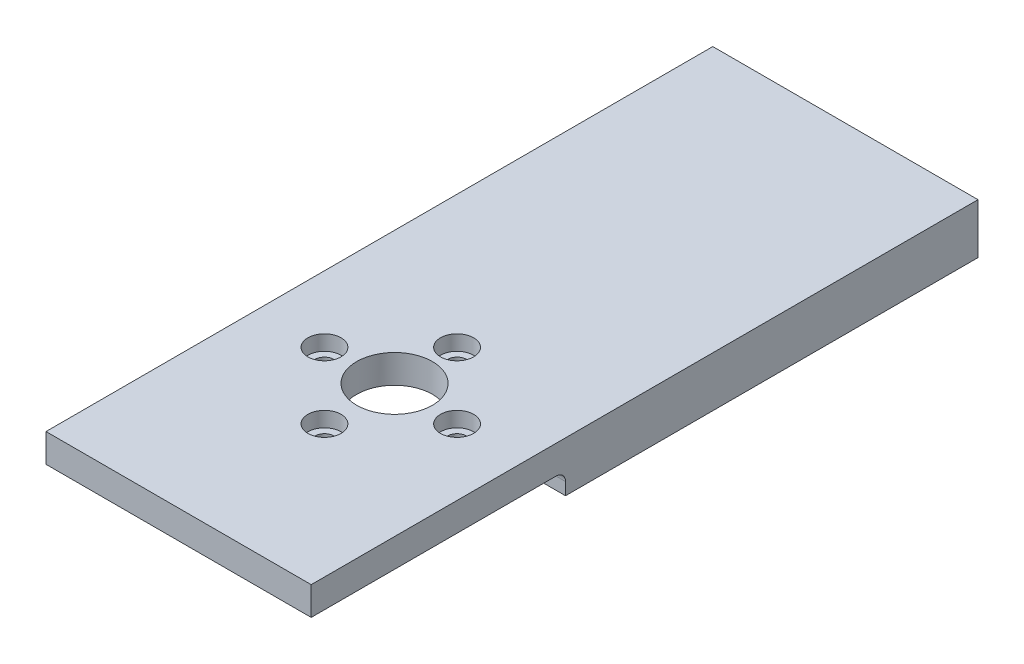
SolidWorks part; units mm, degrees
material "Custom Plastic"
ref_plane "Front Plane" through (0, 0, 0) normal (0, 0, 1) x (1, 0, 0)
ref_plane "Top Plane" through (0, 0, 0) normal (0, 1, 0) x (1, 0, 0)
ref_plane "Right Plane" through (0, 0, 0) normal (1, 0, 0) x (0, 0, -1)
sketch "Sketch1" plane through (0, 0, 0) normal (0, 1, 0) x (1, 0, 0)
  line L1 (-14, -35.2) -> (14, -35.2)
  line L2 (-14, -35.2) -> (-14, 35.2)
  line L3 (-14, 35.2) -> (14, 35.2)
  line L4 (14, -35.2) -> (14, 35.2)
  line L5 (-14, -35.2) -> (14, 35.2) construction
  line L6 (-14, 35.2) -> (14, -35.2) construction
  point P0 (0, 0)
  dimension "D1" = 70.4
  dimension "D2" = 28
extrude "Boss-Extrude1" add sketch "Sketch1" along normal blind 3
sketch "Sketch4" plane through (0, 3, 0) normal (0, 1, 0) x (1, 0, 0)
  line L0 (0, -2.5883) -> (0, -23.7562) construction
  line L1 (14, -35.2) -> (14, 35.2) construction
  circle A0 centre (7, -12.8) radius 1
  circle A1 centre (0, -19.8) radius 1
  circle A2 centre (-7, -12.8) radius 1
  circle A4 centre (0, -5.8) radius 1
  circle A9 centre (0, -12.8) radius 7 construction
  point P18 (0, -12.8)
  dimension "D1" = 2
  dimension "D2" = 14
  dimension "D4" = 14
  dimension "D3" = 4
extrude "Cut-Extrude2" cut sketch "Sketch4" against normal blind 10
sketch "Sketch5" plane through (0, 3, 0) normal (0, 1, 0) x (1, 0, 0)
  line L2 (-14, -35.2) -> (14, -35.2) construction
  line L3 (14, -35.2) -> (14, 35.2) construction
  circle A0 centre (0, -12.4) radius 4
  dimension "D1" = 8
  dimension "D2" = 22.8
  dimension "D3" = 14
extrude "Cut-Extrude3" cut sketch "Sketch5" against normal blind 10
sketch "Sketch10" plane through (0, 3, 0) normal (0, 1, 0) x (1, 0, 0)
  circle A0 centre (0, -19.8) radius 1.75
  circle A1 centre (-7, -12.8) radius 1.75
  circle A2 centre (0, -5.8) radius 1.75
  circle A3 centre (7, -12.8) radius 1.75
  dimension "D1" = 3.5
  dimension "D2" = 3.5
  dimension "D3" = 3.5
  dimension "D4" = 3.5
extrude "Cut-Extrude9" cut sketch "Sketch10" against normal blind 1.6
sketch "Sketch11" plane through (0, 0, 0) normal (0, -1, 0) x (1, 0, 0)
  line L0 (9.1434, 8.3506) -> (14, 8.3506)
  line L1 (-9.1434, 8.3506) -> (-14, 8.3506)
  line L4 (14, -35.2) -> (14, 35.2)
  line L5 (14, 35.2) -> (-14, 35.2)
  line L6 (-14, 35.2) -> (-14, -35.2)
  line L7 (-14, -35.2) -> (14, -35.2)
  line L8 (14, -35.2) -> (14, 8.3506)
  line L10 (-14, 8.3506) -> (-14, -35.2)
  line L11 (-14, -35.2) -> (14, -35.2)
  arc A0 (-9.1434, 8.3506) -> (9.1434, 8.3506) centre (0, 12.4) ccw
  dimension "D1" = 20
  dimension "D2" = 0
extrude "Boss-Extrude2" add sketch "Sketch11" along normal blind 2.3
fillet "Fillet1" radius 1 3 edges at (11.5717, 0, 8.3506) (-11.5717, 0, 8.3506) (0, 0, 2.4)
